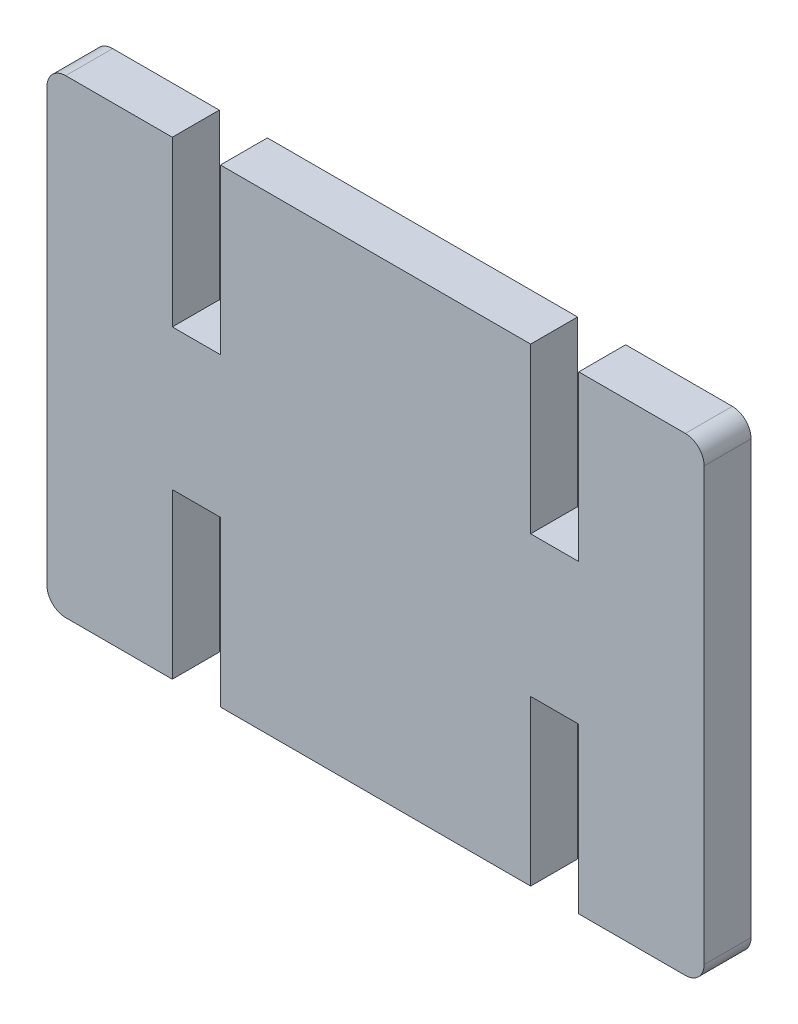
SolidWorks part; units mm, degrees
material "Acrylic (Medium-high impact)"
ref_plane "Front Plane" through (0, 0, 0) normal (0, 0, 1) x (1, 0, 0)
ref_plane "Top Plane" through (0, 0, 0) normal (0, 1, 0) x (1, 0, 0)
ref_plane "Right Plane" through (0, 0, 0) normal (1, 0, 0) x (0, 0, -1)
sketch "Sketch1" plane through (0, 0, 0) normal (0, 0, 1) x (1, 0, 0)
  line L0 (2, 0) -> (68, 0)
  line L1 (0, 2) -> (0, 48)
  line L2 (70, 2) -> (70, 48)
  line L3 (2, 50) -> (68, 50)
  arc A0 (70, 48) -> (68, 50) centre (68, 48) ccw
  arc A1 (0, 48) -> (2, 50) centre (2, 48) cw
  arc A2 (68, 0) -> (70, 2) centre (68, 2) ccw
  arc A3 (0, 2) -> (2, 0) centre (2, 2) ccw
  point P7 (70, 50)
  point P10 (0, 50)
  point P13 (70, 0)
  point P16 (0, 0)
  dimension "D3" = 2
  dimension "D1" = 70
  dimension "D2" = 50
extrude "Boss-Extrude1" add sketch "Sketch1" along normal blind 5
extrude "Cut-Extrude1" cut sketch "Sketch2" against normal blind 5
sketch "Sketch2" plane through (-23.3993, 94.9169, 5) normal (0, 0, 1) x (1, 0, 0)
  line L0 (36.7538, -62.4169) -> (36.7538, -44.9169)
  line L1 (91.3993, -44.9169) -> (25.3993, -44.9169) construction
  line L2 (36.7538, -44.9169) -> (41.8788, -44.9169)
  line L3 (41.8788, -44.9169) -> (41.8788, -62.4169)
  line L4 (36.7538, -62.4169) -> (41.8788, -62.4169)
  line L5 (74.9197, -62.4169) -> (74.9197, -44.9169)
  line L6 (74.9197, -44.9169) -> (80.0447, -44.9169)
  line L7 (80.0447, -44.9169) -> (80.0447, -62.4169)
  line L8 (80.0447, -62.4169) -> (74.9197, -62.4169)
  line L9 (77.4822, -44.9169) -> (77.4822, -62.4169) construction
  line L10 (39.3163, -44.9169) -> (39.3163, -62.4169) construction
  line L11 (58.3993, -44.9169) -> (58.3993, -94.9169) construction
  line L12 (25.3993, -94.9169) -> (91.3993, -94.9169) construction
  line L13 (36.7538, -94.9169) -> (36.7538, -77.4169)
  line L14 (36.7538, -94.9169) -> (41.8788, -94.9169)
  line L15 (36.7538, -77.4169) -> (41.8788, -77.4169)
  line L16 (41.8788, -94.9169) -> (41.8788, -77.4169)
  line L17 (74.9197, -94.9169) -> (74.9197, -77.4169)
  line L18 (74.9197, -94.9169) -> (80.0447, -94.9169)
  line L19 (74.9197, -77.4169) -> (80.0447, -77.4169)
  line L20 (80.0447, -94.9169) -> (80.0447, -77.4169)
  line L21 (23.3993, -69.9169) -> (93.3993, -69.9169) construction
  line L22 (23.3993, -46.9169) -> (23.3993, -92.9169) construction
  line L23 (93.3993, -92.9169) -> (93.3993, -46.9169) construction
  dimension "D1" = 5.125
  dimension "D3" = 38.1659
  dimension "D4" = 15
